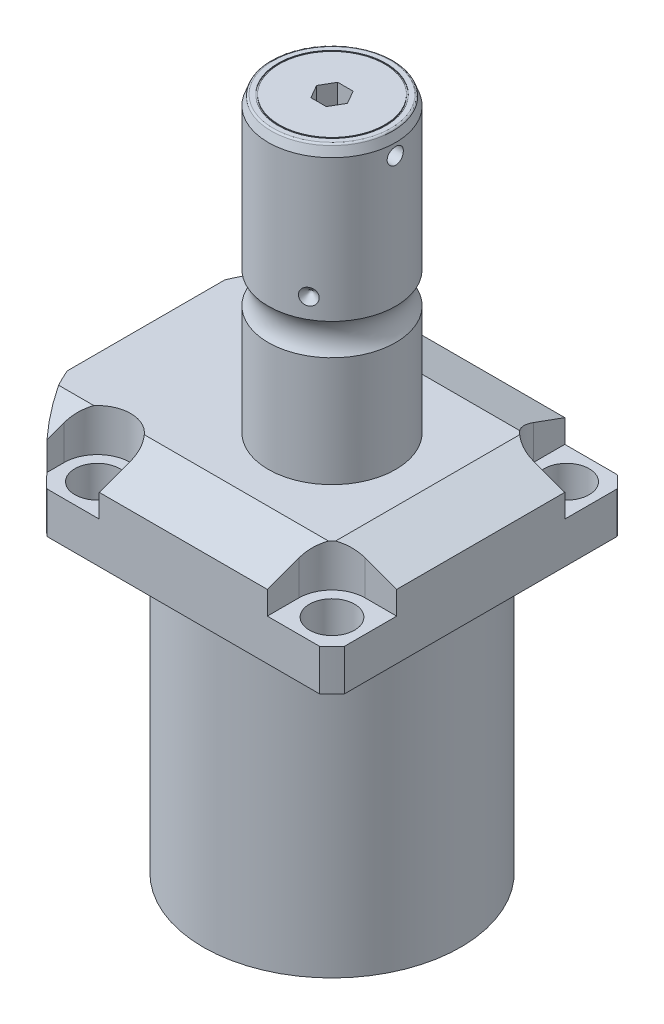
SolidWorks part; units mm, degrees
material "Alloy Steel"
ref_plane "Front Plane" through (0, 0, 0) normal (0, 0, 1) x (1, 0, 0)
ref_plane "Top Plane" through (0, 0, 0) normal (0, 1, 0) x (1, 0, 0)
ref_plane "Right Plane" through (0, 0, 0) normal (1, 0, 0) x (0, 0, -1)
ref_plane "Plane1" through (0, 0, 0) normal (0, 1, 0) x (0, 0, 1)
sketch "Sketch1" plane through (0, 0, 0) normal (0, 1, 0) x (0, 0, 1)
  line L0 (-44.45, 44.45) -> (44.45, 44.45)
  line L1 (44.45, 44.45) -> (44.45, -55.5498)
  line L2 (44.45, -55.5498) -> (-44.45, -55.5498)
  line L3 (-44.45, -55.5498) -> (-44.45, 44.45)
  line L4 (0, 0) -> (0, -60.6467) construction
  dimension "D1" = 55.5498
  dimension "D2" = 99.9998
  dimension "D3" = 88.9
extrude "Extrude1" add sketch "Sketch1" along normal blind 113.919
sketch "Sketch2" plane through (0, 0, 0) normal (0, -1, 0) x (1, 0, 0)
  circle A0 centre (0, 0) radius 60.325
  dimension "D1" = 120.65
extrude "Cut-Extrude1" cut sketch "Sketch2" against normal through all flip side to cut
ref_plane "Plane2" through (0, 0, 0) normal (1, 0, 0) x (0, 0, 1)
sketch "Sketch3" plane through (0, 0, 0) normal (1, 0, 0) x (0, 0, 1)
  line L0 (38.4937, 0) -> (38.4937, -88.9)
  line L1 (38.4937, -88.9) -> (76.5937, -88.9)
  line L2 (76.5937, -88.9) -> (76.5937, 0)
  line L3 (76.5937, 0) -> (38.4937, 0)
  line L4 (0, -93.345) -> (0, 4.445) construction
  line L5 (40.7836, 0) -> (-40.7836, 0) construction
  dimension "D1" = 76.9874
  dimension "D2" = 153.1874
  dimension "D3" = 88.9
revolve "Cut-Revolve1" cut sketch "Sketch3" angle 360 about L4
fillet "Fillet1" radius 0.381 1 edges at (0, 88.9, 38.4937)
sketch "Sketch4" plane through (0, 113.919, 0) normal (0, 1, 0) x (-1, 0, 0)
  line L0 (-44.45, 40.7836) -> (-44.45, -40.7836) construction
  line L1 (40.7836, 44.45) -> (-40.7836, 44.45) construction
  line L2 (-25.1206, -44.45) -> (-25.1206, -35.052)
  line L3 (-44.45, -44.45) -> (-25.1206, -44.45)
  line L4 (-44.45, -25.1206) -> (-44.45, -44.45)
  line L5 (-35.052, -25.1206) -> (-44.45, -25.1206)
  line L6 (44.9834, -44.45) -> (25.1206, -44.45)
  line L7 (25.1206, 44.45) -> (25.1206, 35.052)
  line L8 (44.9834, 44.45) -> (44.9834, 35.052)
  line L9 (44.9834, 44.45) -> (25.1206, 44.45)
  line L10 (-35.052, 25.1206) -> (-44.45, 25.1206)
  line L11 (-44.45, 25.1206) -> (-44.45, 44.45)
  line L12 (-44.45, 44.45) -> (-25.1206, 44.45)
  line L13 (-25.1206, 44.45) -> (-25.1206, 35.052)
  line L14 (-48.9217, 0) -> (49.4551, 0) construction
  line L15 (44.9834, -44.45) -> (44.9834, -35.052)
  line L16 (25.1206, -44.45) -> (25.1206, -35.052)
  arc A0 (25.1206, -35.052) -> (44.9834, -35.052) centre (35.052, -35.052) cw
  arc A1 (-35.052, -25.1206) -> (-25.1206, -35.052) centre (-35.052, -35.052) cw
  arc A2 (-35.052, 25.1206) -> (-25.1206, 35.052) centre (-35.052, 35.052) ccw
  arc A3 (25.1206, 35.052) -> (44.9834, 35.052) centre (35.052, 35.052) ccw
  dimension "D2" = 9.9314
  dimension "D1" = 35.052
  dimension "D3" = 35.052
  dimension "D4" = 35.052
extrude "Cut-Extrude2" cut sketch "Sketch4" against normal blind 12.7
ref_plane "Plane3" through (0, 0, 0) normal (1, 0, 0) x (0, 0, -1)
sketch "Sketch5" plane through (0, 0, 0) normal (1, 0, 0) x (0, 0, -1)
  line L0 (-28.575, 113.919) -> (-44.45, 108.141)
  line L1 (0, 0) -> (0, 154.1081) construction
  line L2 (-28.575, 113.919) -> (-44.45, 113.919)
  line L3 (-44.45, 113.919) -> (-44.45, 108.141)
  dimension "D1" = 15.875
  dimension "D2" = 20
extrude "Cut-Extrude9" cut sketch "Sketch5" against normal through all and the other way through all
mirror "Mirror1" about plane through (0, 0, 0) normal (0, 0, 1) of "Cut-Extrude9"
ref_plane "Plane7" through (0, 0, 0) normal (0, 0, 1) x (1, 0, 0)
sketch "Sketch9" plane through (0, 0, 0) normal (0, 0, 1) x (1, 0, 0)
  line L0 (28.575, 113.919) -> (44.45, 108.141)
  line L1 (44.45, 108.141) -> (44.45, 113.919)
  line L2 (44.45, 113.919) -> (28.575, 113.919)
  dimension "D1" = 15.875
  dimension "D2" = 20
extrude "Cut-Extrude7" cut sketch "Sketch9" against normal through all and the other way through all
ref_plane "Plane8" through (-41.402, 88.9, -18.1102) normal (1, 0, 0) x (0, 1, 0)
sketch "Sketch20" plane through (-41.402, 88.9, -18.1102) normal (1, 0, 0) x (0, 1, 0)
  line L0 (-88.9, 18.1102) -> (39.8401, 18.1102) construction
  line L1 (-7.2797, 36.2204) -> (36.9042, 36.2204) construction
  line L2 (0, 41.9227) -> (1.4478, 41.9227)
  line L3 (0, 58.8938) -> (0, -22.6734) construction
  line L4 (1.4478, 41.9227) -> (1.4478, 39.4716)
  line L5 (1.4478, 39.4716) -> (2.4638, 39.4716)
  line L6 (2.4638, 39.4716) -> (2.4638, 37.465)
  line L7 (2.4638, 37.465) -> (13.4366, 37.465)
  line L8 (13.4366, 37.465) -> (13.4366, 36.2204)
  line L9 (13.4366, 36.2204) -> (0, 36.2204)
  line L10 (0, 41.9227) -> (0, 36.2204)
  dimension "D1" = 18.1102
  dimension "D2" = 11.4046
  dimension "D3" = 1.4478
  dimension "D4" = 6.5024
  dimension "D5" = 1.016
  dimension "D6" = 2.4892
  dimension "D7" = 10.9728
revolve "Cut-Revolve4" cut sketch "Sketch20" angle 360 about L1
mirror "Mirror10" about plane through (0, 0, 0) normal (0, 0, 1) of "Cut-Revolve4"
sketch "Sketch10" plane through (-41.402, 88.9, -18.1102) normal (1, 0, 0) x (0, 1, 0)
  line L0 (-1.0325, 0) -> (1.5659, 0) construction
  line L1 (13.4366, 1.2446) -> (2.4638, 1.2446) construction
  line L2 (2.4638, -1.2446) -> (13.4366, -1.2446) construction
  line L3 (0, 58.8938) -> (0, -22.6734) construction
  circle A0 centre (0.2667, 4.5212) radius 1.1811
  dimension "D1" = 2.3622
  dimension "D2" = 0.2667
  dimension "D3" = 9.0424
revolve "Revolve4" add sketch "Sketch10" angle 360 about L0
ref_plane "Plane9" through (-41.402, 88.9, 18.1102) normal (1, 0, 0) x (0, 1, 0)
sketch "Sketch11" plane through (-41.402, 88.9, 18.1102) normal (1, 0, 0) x (0, 1, 0)
  line L0 (-1.0325, 0) -> (1.5659, 0) construction
  line L1 (13.4366, 1.2446) -> (2.4638, 1.2446) construction
  line L3 (0, 22.6734) -> (0, -58.8938) construction
  line L4 (2.4638, -1.2446) -> (13.4366, -1.2446) construction
  circle A0 centre (0.2667, 4.5212) radius 1.1811
  point P10 (0, 0)
  dimension "D1" = 2.3622
  dimension "D2" = 9.0424
  dimension "D3" = 0.2667
revolve "Revolve2" add sketch "Sketch11" angle 360 about L0
ref_plane "Plane10" through (-55.5498, 101.9048, 12.9794) normal (0, 0, 1) x (0, 1, 0)
sketch "S2D0007" plane through (-55.5498, 101.9048, 12.9794) normal (0, 0, 1) x (0, 1, 0)
  line L0 (0, 0) -> (10.4775, 0)
  line L1 (10.4775, 0) -> (10.4775, -0.254)
  line L2 (10.4775, -0.254) -> (6.1849, -0.254)
  line L3 (6.1849, -0.254) -> (5.6423, -2.8067)
  line L4 (5.6423, -2.8067) -> (4.9784, -3.4706)
  line L5 (4.9784, -3.4706) -> (4.9784, -14.224)
  line L6 (4.9784, -14.224) -> (0, -14.224)
  line L7 (0, -14.224) -> (0, 0)
  line L8 (0, -14.9352) -> (0, 0.7112) construction
  line L9 (-13.0048, 0) -> (-13.0048, -14.7662) construction
  dimension "D1" = 0.254
  dimension "D2" = 13.0048
revolve "Cut-Revolve2" cut sketch "S2D0007" angle 360 about L8
ref_plane "Plane11" through (-55.5498, 101.9048, -12.9794) normal (0, 0, 1) x (0, 1, 0)
sketch "Sketch13" plane through (-55.5498, 101.9048, -12.9794) normal (0, 0, 1) x (0, 1, 0)
  line L0 (0, 0) -> (10.4775, 0)
  line L1 (10.4775, 0) -> (10.4775, -0.254)
  line L2 (10.4775, -0.254) -> (6.1849, -0.254)
  line L3 (6.1849, -0.254) -> (5.6423, -2.8067)
  line L4 (5.6423, -2.8067) -> (4.9784, -3.4706)
  line L5 (4.9784, -3.4706) -> (4.9784, -14.224)
  line L6 (4.9784, -14.224) -> (0, -14.224)
  line L7 (0, -14.224) -> (0, 0)
  line L8 (0, -14.9352) -> (0, 0.7112) construction
  line L9 (-13.0048, 0) -> (-13.0048, -14.7662) construction
  dimension "D1" = 0.254
  dimension "D2" = 13.0048
revolve "Cut-Revolve3" cut sketch "Sketch13" angle 360 about L8
sketch "Sketch14" plane through (-55.2958, 0, 0) normal (-1, 0, 0) x (0, 0, 1)
  circle A0 centre (-12.9794, 101.9048) radius 7.112
  circle A1 centre (-12.9794, 101.9048) radius 4.9784 construction
  dimension "D1" = 14.224
extrude "Extrude2" add sketch "Sketch14" along normal blind 1.27
ref_plane "Plane12" through (0, 0, 0) normal (1, 0, 0) x (0, -1, 0)
sketch "Sketch15" plane through (0, 0, 0) normal (1, 0, 0) x (0, -1, 0)
  line L0 (-113.919, 0) -> (-113.919, 19.05)
  line L1 (-113.919, 19.05) -> (-146.7531, 19.05)
  line L2 (-156.1673, 19.05) -> (-198.5264, 19.05)
  line L3 (-201.4474, 17.9868) -> (-201.4474, 0)
  line L4 (-201.4474, 0) -> (-113.919, 0)
  line L5 (-197.6361, 0) -> (-64.6704, 0) construction
  line L6 (-113.919, 27.5233) -> (-113.919, -27.5233) construction
  line L7 (-88.9, 40.7836) -> (-88.9, 44.45) construction
  line L8 (-198.5264, 19.05) -> (-201.4474, 17.9868)
  arc A0 (-156.1673, 19.05) -> (-146.7531, 19.05) centre (-151.4602, 25.4254) ccw
  dimension "D2" = 20
  dimension "D4" = 7.9248
  dimension "D6" = 35.0012
  dimension "D1" = 112.5474
  dimension "D3" = 38.1
  dimension "D5" = 49.9872
  dimension "D7" = 2.921
revolve "Revolve3" add sketch "Sketch15" angle 360 about L5
ref_plane "Plane13" through (0, 0, 0) normal (0, 0, -1) x (0, -1, 0)
hole_wizard "Hole1" positions "Sketch18" profile "Sketch17" legacy end condition up to next
sketch "Sketch18" plane through (0, 101.219, 0) normal (0, 1, 0) x (-1, 0, 0)
  arc A0 (44.9834, -35.052) -> (25.1206, -35.052) centre (35.052, -35.052) ccw construction
  arc A1 (25.1206, 35.052) -> (44.9834, 35.052) centre (35.052, 35.052) ccw construction
  arc A2 (-35.052, 25.1206) -> (-25.1206, 35.052) centre (-35.052, 35.052) ccw construction
  arc A3 (-25.1206, -35.052) -> (-35.052, -25.1206) centre (-35.052, -35.052) ccw construction
  point P0 (-35.052, -35.052)
  point P1 (-35.052, 35.052)
  point P3 (35.052, 35.052)
  point P5 (35.052, -35.052)
sketch "Sketch17" plane through (35.052, 101.219, -35.052) normal (1, 0, 0) x (0, 0, 1)
  line L0 (0, 0) -> (0, 12.319)
  line L1 (0, 12.319) -> (6.7437, 12.319)
  line L2 (6.7437, 12.319) -> (6.7437, 0)
  line L3 (6.7437, 0) -> (0, 0)
  line L4 (0, 110) -> (0, -10) construction
  dimension "Diameter" = 13.4874
  dimension "Depth" = 12.319
chamfer "Chamfer1" distance 0.635 angle 45 2 edges at (-41.402, 91.3638, 16.8656) (-41.402, 91.3638, -16.8656)
fillet "Fillet2" radius 0.635 1 edges at (0, 201.4474, 17.9868)
sketch "Sketch21" plane through (0, 201.4474, 0) normal (0, 1, 0) x (1, 0, 0)
  circle A0 centre (0, 0) radius 16.129
  circle A1 centre (0, 0) radius 15.748
  dimension "D1" = 31.496
  dimension "D2" = 32.258
extrude "Cut-Extrude10" cut sketch "Sketch21" against normal blind 0.254
sketch "Sketch22" plane through (0, 201.4474, 0) normal (0, 1, 0) x (1, 0, 0)
  line L1 (4.6188, 0) -> (2.3094, 4)
  line L2 (2.3094, 4) -> (-2.3094, 4)
  line L3 (-2.3094, 4) -> (-4.6188, 0)
  line L4 (-4.6188, 0) -> (-2.3094, -4)
  line L5 (-2.3094, -4) -> (2.3094, -4)
  line L6 (2.3094, -4) -> (4.6188, 0)
  circle A0 centre (0, 0) radius 4 construction
  dimension "D1" = 8
extrude "Cut-Extrude11" cut sketch "Sketch22" against normal blind 7.9756
sketch "Sketch23" plane through (0, 0, 0) normal (0, 0, 1) x (1, 0, 0)
  line L0 (7.8373, 162.1282) -> (-56.125, 162.1282) construction
  line L1 (-19.05, 164.5412) -> (-16.637, 162.1282)
  line L3 (-19.05, 198.5264) -> (-19.05, 156.1673) construction
  line L4 (-16.637, 162.1282) -> (-19.05, 162.1282)
  line L5 (-19.05, 162.1282) -> (-19.05, 164.5412)
  arc A0 (19.05, 156.1673) -> (19.05, 146.7531) centre (25.4254, 151.4602) ccw construction
  dimension "D3" = 10.668
  dimension "D1" = 4.826
  dimension "D2" = 45
revolve "Cut-Revolve5" cut sketch "Sketch23" angle 360 about L0
pattern_circular "CirPattern1" count 3 over 360 about axis through (0, 197.6361, 0) along (0, 1, 0) of "Cut-Revolve5"
sketch "Sketch24" plane through (0, 0, 0) normal (0, 0, 1) x (1, 0, 0)
  line L0 (3.2512, 195.0974) -> (47.4739, 195.0974) construction
  line L2 (19.05, 197.5104) -> (15.24, 197.5104)
  line L3 (19.05, 197.5104) -> (19.05, 195.0974)
  line L4 (19.05, 195.0974) -> (15.24, 195.0974)
  line L5 (15.24, 197.5104) -> (15.24, 195.0974)
  line L6 (17.5422, 201.4474) -> (-17.5422, 201.4474) construction
  line L7 (19.05, 156.1673) -> (19.05, 198.5264) construction
  dimension "D1" = 3.81
  dimension "D2" = 4.826
  dimension "D3" = 6.35
revolve "Cut-Revolve6" cut sketch "Sketch24" angle 360 about L0
